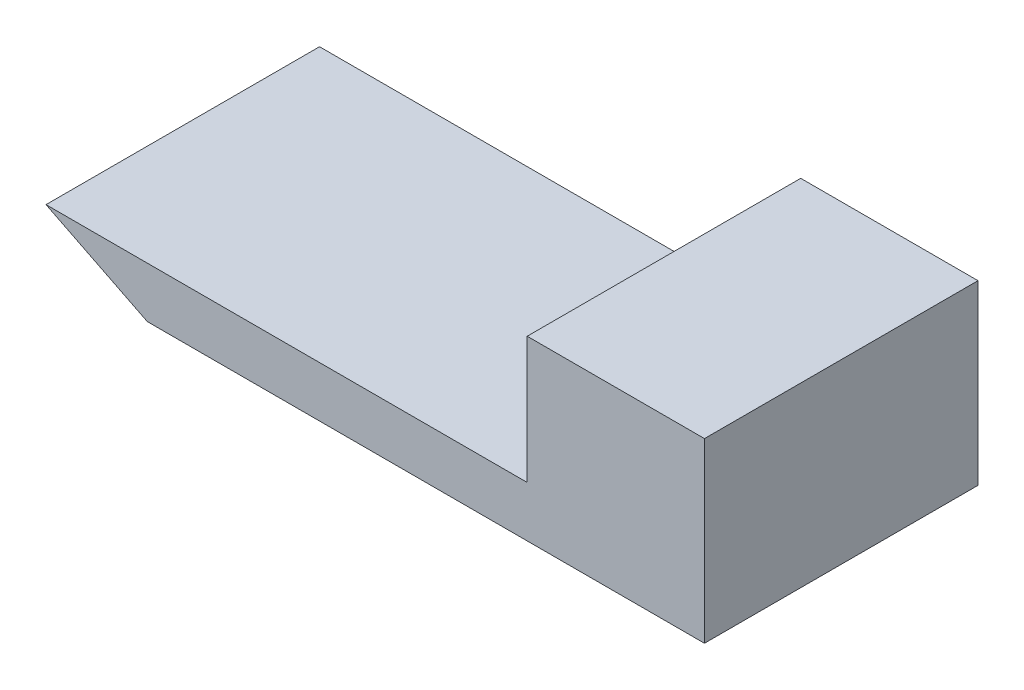
SolidWorks part; units mm, degrees
ref_plane "Alzado" through (0, 0, 0) normal (0, 0, 1) x (1, 0, 0)
ref_plane "Planta" through (0, 0, 0) normal (0, 1, 0) x (1, 0, 0)
ref_plane "Vista lateral" through (0, 0, 0) normal (1, 0, 0) x (0, 0, -1)
sketch "Croquis1" plane through (0, 0, 0) normal (0, 0, 1) x (1, 0, 0)
  line L1 (-41.3861, 15.4543) -> (-41.3861, 13.4543)
  line L2 (-41.3861, 13.4543) -> (-63.3861, 13.4543)
  line L3 (-67.3861, 15.4543) -> (-63.3861, 13.4543)
  line L4 (-41.3861, 15.4543) -> (-41.3861, 20.4543)
  line L5 (-41.3861, 20.4543) -> (-48.3861, 20.4543)
  line L6 (-48.3861, 20.4543) -> (-48.3861, 15.4543)
  line L7 (-48.3861, 15.4543) -> (-67.3861, 15.4543)
extrude "Saliente-Extruir1" add sketch "Croquis1" along normal blind 10.8
